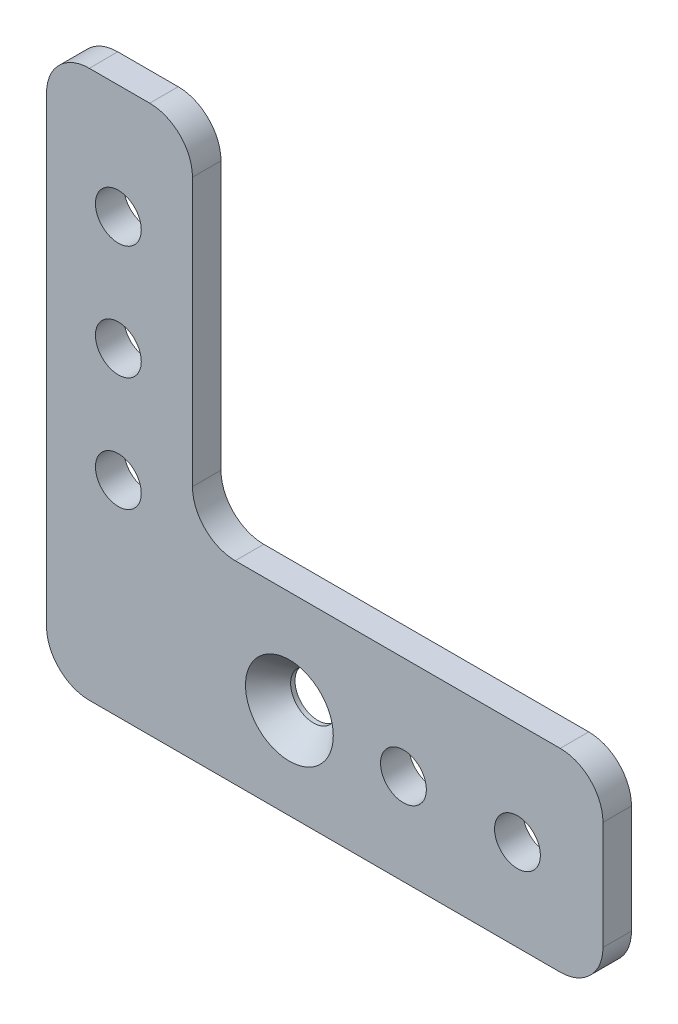
SolidWorks part; units mm, degrees
material "6061-T6 (SS)"
ref_plane "Front Plane" through (0, 0, 0) normal (0, 0, 1) x (1, 0, 0)
ref_plane "Top Plane" through (0, 0, 0) normal (0, 1, 0) x (1, 0, 0)
ref_plane "Right Plane" through (0, 0, 0) normal (1, 0, 0) x (0, 0, -1)
sketch "Sketch1" plane through (0, 0, 0) normal (0, 0, 1) x (1, 0, 0)
  line L0 (34.925, -19.05) -> (-27.051, -19.05) construction
  line L1 (-34.925, -31.75) -> (34.925, -31.75)
  line L2 (-34.925, -31.75) -> (-34.925, 31.75)
  line L3 (-34.925, 31.75) -> (34.925, 31.75)
  line L4 (34.925, -31.75) -> (34.925, 31.75)
  line L5 (-34.925, -31.75) -> (34.925, 31.75) construction
  line L6 (-34.925, 31.75) -> (34.925, -31.75) construction
  line L7 (34.925, 31.75) -> (-10.795, 31.75)
  line L8 (34.925, 31.75) -> (34.925, -7.62)
  line L9 (34.925, -7.62) -> (-10.795, -7.62)
  line L10 (-10.795, 31.75) -> (-10.795, -7.62)
  line L11 (-34.925, -31.75) -> (-27.051, -31.75)
  line L12 (-34.925, -31.75) -> (-34.925, 31.75)
  line L13 (-34.925, 31.75) -> (-27.051, 31.75)
  line L14 (-27.051, -31.75) -> (-27.051, 31.75)
  line L15 (-27.051, -31.75) -> (34.925, -31.75)
  line L16 (-27.051, -31.75) -> (-27.051, -29.21)
  line L17 (-27.051, -29.21) -> (34.925, -29.21)
  line L18 (34.925, -31.75) -> (34.925, -29.21)
  circle A0 centre (-19.05, -19.05) radius 2.5527
  circle A1 centre (-19.05, -6.35) radius 2.5527
  circle A2 centre (-19.05, 6.35) radius 2.5527
  circle A3 centre (-19.05, 19.05) radius 2.5527
  circle A4 centre (12.7, -19.05) radius 2.5527
  circle A5 centre (25.4, -19.05) radius 2.5527
  point P0 (0, 0)
  point P22 (25.4, -19.05)
  point P23 (0, -19.05)
  point P24 (12.7, -19.05)
  dimension "D7" = 5.1054
  dimension "D1" = 69.85
  dimension "D2" = 63.5
  dimension "D3" = 24.13
  dimension "D4" = 24.13
  dimension "D5" = 7.874
  dimension "D6" = 63.5
  dimension "D8" = 15.875
  dimension "D9" = 12.7
  dimension "D10" = 12.7
  dimension "D11" = 12.7
  dimension "D12" = 12.7
  dimension "D13" = 12.7
  dimension "D14" = 12.7
  dimension "D15" = 27.051
  dimension "D16" = 2.54
extrude "Boss-Extrude1" add sketch "Sketch1" along normal blind 3.175
fillet "Fillet1" radius 4.7625 6 edges at (-27.051, 31.75, 1.5875) (-10.795, 31.75, 1.5875) (-10.795, -7.62, 1.5875) (34.925, -7.62, 1.5875) (34.925, -29.21, 1.5875) (-27.051, -29.21, 1.5875)
hole_wizard "CSK for #10 Flat Head Machine Screw1" positions "Sketch3" profile "Sketch2" countersink size "#10" standard "ANSI Inch" end condition through all
sketch "Sketch3" plane through (0, 0, 3.175) normal (0, 0, 1) x (1, 0, 0)
  point P0 (0, -19.05)
  point P11 (0, 0)
  point P12 (0, 0)
sketch "Sketch2" plane through (0, -19.05, 3.175) normal (1, 0, 0) x (0, -1, 0)
  line L0 (0, 0) -> (0, 3.175)
  line L1 (0, 3.175) -> (2.5527, 3.175)
  line L2 (2.5527, 3.175) -> (2.5527, 2.6882)
  line L3 (2.5527, 2.6882) -> (4.8895, 0)
  line L5 (4.8895, 0) -> (0, 0)
  line L6 (-2.5527, 2.6882) -> (-4.8895, 0) construction
  line L11 (0, -6.35) -> (0, 107.95) construction
  dimension "Thru Hole Dia." = 5.1054
  dimension "Thru Hole Depth" = 3.175
  dimension "Near C'Sink Dia." = 9.779
  dimension "Near C'Sink Angle" = 82
